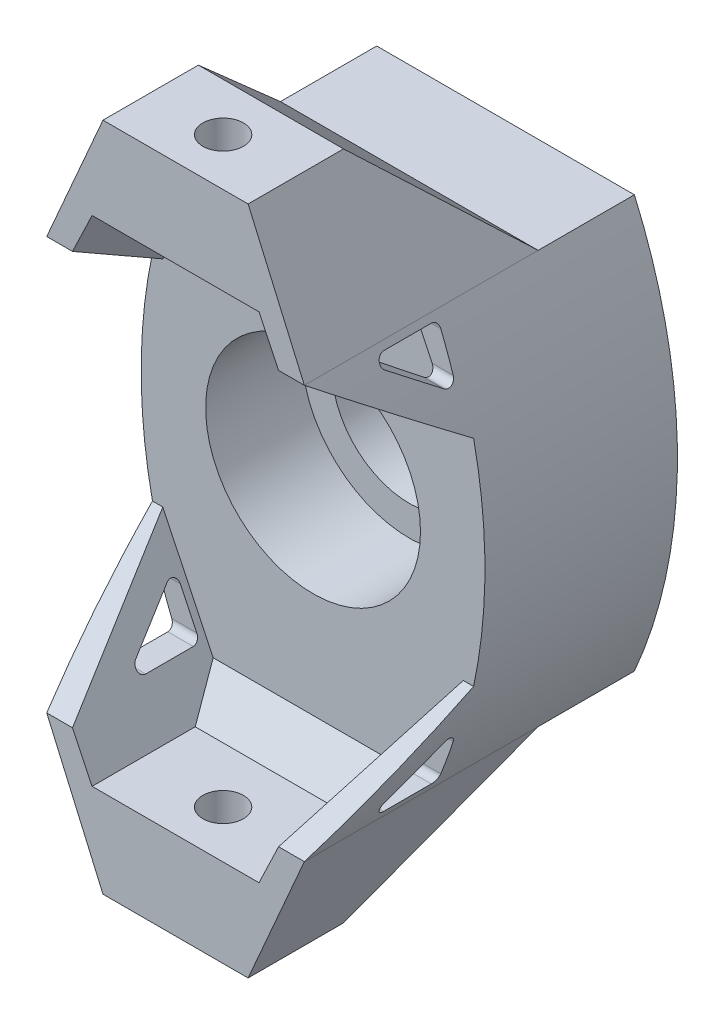
SolidWorks part; units mm, degrees
material "ABS"
ref_plane "Front Plane" through (0, 0, 0) normal (0, 0, 1) x (1, 0, 0)
ref_plane "Top Plane" through (0, 0, 0) normal (0, 1, 0) x (1, 0, 0)
ref_plane "Right Plane" through (0, 0, 0) normal (1, 0, 0) x (0, 0, -1)
sketch "Sketch1" plane through (0, 0, 0) normal (0, 0, 1) x (1, 0, 0)
  line L0 (-9.5192, 15.24) -> (9.5192, 15.24)
  line L1 (-26.1092, 0) -> (27.3943, 0) construction
  line L2 (0, 24.1129) -> (0, -26.203) construction
  line L3 (-9.5192, -15.24) -> (9.5192, -15.24)
  line L4 (-9.5192, 15.24) -> (-5.3622, 24.765)
  line L5 (-5.3622, 24.765) -> (5.3622, 24.765)
  line L6 (5.3622, 24.765) -> (9.5192, 15.24)
  line L7 (5.3622, -24.765) -> (9.5192, -15.24)
  line L8 (-5.3622, -24.765) -> (5.3622, -24.765)
  line L9 (-9.5192, -15.24) -> (-5.3622, -24.765)
  circle A0 centre (0, 0) radius 3.175
  circle A1 centre (0, 0) radius 7.9375
  arc A3 (-9.5192, 15.24) -> (-9.5192, -15.24) centre (25.4, 0) ccw
  arc A4 (9.5192, 15.24) -> (9.5192, -15.24) centre (-25.4, 0) cw
  point P4 (12.7, 0)
  point P14 (-12.7, 0)
  dimension "D1" = 6.35
  dimension "D2" = 15.875
  dimension "D3" = 38.1
  dimension "D5" = 38.1
  dimension "D7" = 12.7
  dimension "D4" = 15.24
  dimension "D6" = 12.7
  dimension "D8" = 9.525
extrude "Boss-Extrude1" add sketch "Sketch1" along normal blind 7.112 contours A4 L0 A3 L3 A1 | L6 L5 L4 L0 | L3 L9 L8 L7
sketch "Sketch2" plane through (0, 0, 0) normal (0, 0, -1) x (-1, 0, 0)
  line L0 (9.5192, -15.24) -> (-9.5192, -15.24) construction
  line L1 (9.5192, 15.24) -> (-9.5192, 15.24) construction
  line L2 (9.5192, -15.24) -> (-9.5192, -15.24)
  line L3 (9.5192, 15.24) -> (-9.5192, 15.24)
  line L6 (-9.5192, -15.24) -> (-5.3622, -24.765)
  line L7 (-5.3622, -24.765) -> (5.3622, -24.765)
  line L8 (5.3622, -24.765) -> (9.5192, -15.24)
  line L9 (9.5192, 15.24) -> (5.3622, 24.765)
  line L10 (5.3622, 24.765) -> (-5.3622, 24.765)
  line L11 (-5.3622, 24.765) -> (-9.5192, 15.24)
  line L12 (-9.5192, -15.24) -> (-5.3622, -24.765)
  line L13 (-5.3622, -24.765) -> (5.3622, -24.765)
  line L14 (5.3622, -24.765) -> (9.5192, -15.24)
  line L15 (9.5192, 15.24) -> (5.3622, 24.765)
  line L16 (5.3622, 24.765) -> (-5.3622, 24.765)
  line L17 (-5.3622, 24.765) -> (-9.5192, 15.24)
  arc A2 (-9.5192, 15.24) -> (-9.5192, -15.24) centre (25.4, 0) ccw
  arc A3 (9.5192, -15.24) -> (9.5192, 15.24) centre (-25.4, 0) ccw
  arc A4 (-9.5192, 15.24) -> (-9.5192, -15.24) centre (25.4, 0) ccw
  arc A5 (9.5192, -15.24) -> (9.5192, 15.24) centre (-25.4, 0) ccw
  circle A6 centre (0, 0) radius 5.715
  circle A8 centre (0, 0) radius 3.175 construction
  circle A9 centre (0, 0) radius 3.175
  dimension "D2" = 2.54
  dimension "D1" = 0
extrude "Boss-Extrude2" add sketch "Sketch2" along normal blind 7.112
sketch "Sketch3" plane through (0, 0, 7.112) normal (0, 0, 1) x (1, 0, 0)
  line L0 (5.3622, 24.765) -> (9.5192, 15.24) construction
  line L1 (-5.3622, 24.765) -> (5.3622, 24.765) construction
  line L2 (0, 24.1129) -> (0, -26.203) construction
  line L3 (-9.5192, 15.24) -> (9.5192, 15.24) construction
  line L4 (-9.5192, 15.24) -> (-5.3622, 24.765) construction
  line L5 (5.3622, 24.765) -> (9.5192, 15.24)
  line L6 (-5.3622, 24.765) -> (5.3622, 24.765)
  line L7 (0, 24.1129) -> (0, -26.203)
  line L8 (-9.5192, 15.24) -> (9.5192, 15.24)
  line L9 (-9.5192, 15.24) -> (-5.3622, 24.765)
  line L10 (5.3622, -24.765) -> (9.5192, -15.24) construction
  line L11 (-5.3622, -24.765) -> (5.3622, -24.765) construction
  line L12 (-9.5192, -15.24) -> (-5.3622, -24.765) construction
  line L13 (-9.5192, -15.24) -> (9.5192, -15.24) construction
  line L14 (5.3622, -24.765) -> (9.5192, -15.24)
  line L15 (-5.3622, -24.765) -> (5.3622, -24.765)
  line L16 (-9.5192, -15.24) -> (-5.3622, -24.765)
  line L17 (-9.5192, -15.24) -> (9.5192, -15.24)
extrude "Boss-Extrude3" add sketch "Sketch3" along normal blind 10.16
sketch "Sketch4" plane through (0, 24.765, 0) normal (0, 1, 0) x (1, 0, 0)
  line L0 (0, 0) -> (0, -17.272) construction
  line L1 (5.3622, -17.272) -> (-5.3622, -17.272) construction
  line L2 (-5.3622, -13.7567) -> (5.3622, -13.7567) construction
  line L3 (-5.3622, -17.272) -> (-5.3622, 0) construction
  line L4 (5.3622, -17.272) -> (5.3622, 0) construction
  circle A0 centre (0, -13.7567) radius 1.5
  dimension "D2" = 3
  dimension "D1" = 3.5153
extrude "Cut-Extrude1" cut sketch "Sketch4" against normal through all
sketch3d "3DSketch1"
  line L1 (-9.5192, 15.24, 17.272) -> (-9.5192, 15.24, 7.112) construction
sketch "Sketch5" plane through (-9.5192, 0, 0) normal (-1, 0, 0) x (0, 0, 1)
  line L0 (17.272, 24.765) -> (17.272, 15.24) construction
  line L1 (7.112, 15.24) -> (0, 15.24) construction
  line L2 (17.272, 15.24) -> (7.112, 15.24) construction
  line L3 (17.272, 24.765) -> (0, 24.765) construction
  line L4 (0, 24.765) -> (0, 15.24) construction
  line L5 (17.272, 24.765) -> (17.272, 15.24)
  line L6 (7.112, 15.24) -> (0, 15.24)
  line L7 (17.272, 15.24) -> (7.112, 15.24)
  line L8 (17.272, 24.765) -> (0, 24.765)
  line L9 (0, 24.765) -> (0, 15.24)
  line L10 (15.2567, 24.765) -> (12.2567, 24.765) construction
  line L11 (15.2567, 24.765) -> (12.2567, 24.765)
  line L12 (12.2567, 24.765) -> (10.2247, 24.765)
  line L13 (17.272, 18.2651) -> (9.652, 18.2651)
  line L14 (7.112, 15.7251) -> (7.112, 15.24)
  line L15 (7.112, 15.7251) -> (9.652, 18.2651)
  line L16 (0, 15.24) -> (10.2247, 24.765)
  dimension "D5" = 45
  dimension "D1" = 2.0153
  dimension "D2" = 2.032
  dimension "D4" = 6.4999
  dimension "D6" = 2.54
extrude "Cut-Extrude2" cut sketch "Sketch5" against normal through all contours L9 L16 L8 | L15 L14 L7 L5 L13
sketch "Sketch6" plane through (0, 0, 7.112) normal (0, 0, 1) x (1, 0, 0)
  line L0 (-9.5192, 15.24) -> (9.5192, 15.24) construction
  line L1 (-9.5192, 15.24) -> (9.5192, 15.24)
  line L2 (-11.864, 7.9375) -> (11.864, 7.9375)
  line L3 (-6.1669, 18.2651) -> (-6.1669, 7.9375)
  line L4 (6.1669, 18.2651) -> (6.1669, 7.9375)
  line L5 (8.1989, 18.2651) -> (-8.1989, 18.2651) construction
  line L6 (8.1989, 18.2651) -> (-8.1989, 18.2651)
  line L7 (-9.3075, 15.7251) -> (-8.1989, 18.2651) construction
  line L8 (-9.3075, 15.7251) -> (-9.5192, 15.24) construction
  line L9 (-9.3075, 15.7251) -> (-8.1989, 18.2651)
  line L10 (-9.3075, 15.7251) -> (-9.5192, 15.24)
  line L11 (8.1989, 18.2651) -> (9.3075, 15.7251) construction
  line L12 (9.5192, 15.24) -> (9.3075, 15.7251) construction
  line L13 (8.1989, 18.2651) -> (9.3075, 15.7251)
  line L14 (9.5192, 15.24) -> (9.3075, 15.7251)
  line L15 (-11.102, 7.9375) -> (-6.1669, 18.2651)
  line L16 (6.1669, 18.2651) -> (11.102, 7.9375)
  arc A0 (9.5192, -15.24) -> (9.5192, 15.24) centre (-25.4, 0) ccw construction
  arc A1 (-9.5192, 15.24) -> (-9.5192, -15.24) centre (25.4, 0) ccw construction
  arc A2 (9.5192, -15.24) -> (9.5192, 15.24) centre (-25.4, 0) ccw
  arc A3 (-9.5192, 15.24) -> (-9.5192, -15.24) centre (25.4, 0) ccw
  circle A4 centre (0, 0) radius 7.9375 construction
  circle A5 centre (0, 0) radius 7.9375
  arc M3 (9.5192, -15.24) -> (9.5192, 15.24) centre (-25.4, 0) ccw
  line M4 (9.5192, 15.24) -> (9.3075, 15.7251)
  line M5 (9.3075, 15.7251) -> (-9.3075, 15.7251)
  line M6 (-9.3075, 15.7251) -> (-9.5192, 15.24)
  arc M7 (-9.5192, 15.24) -> (-9.5192, -15.24) centre (25.4, 0) ccw
  dimension "D1" = 2.032
  dimension "D2" = 2.032
  dimension "D3" = 0.762
  dimension "D4" = 0.762
extrude "Boss-Extrude5" add sketch "Sketch6" along normal up to surface (10.16 mm away) contours L2 L15 L1 M7 | L1 L15 M5 M6 | L15 L6 L9 M5 | L6 L16 L13 M5 | L16 L1 M5 M4 | L1 L16 L2 M3 up to face at (0, 21.5151, 17.272)
sketch "Sketch7" plane through (-9.5192, 0, 0) normal (-1, 0, 0) x (0, 0, 1)
  line L0 (7.112, 7.9375) -> (7.112, 15.24)
  line L1 (17.272, 15.24) -> (0, 15.24) construction
  line L2 (7.112, 9.7631) -> (14.732, 15.24)
  line L4 (7.112, 7.9375) -> (17.272, 15.24)
  line L11 (17.272, 15.24) -> (17.272, 7.9375)
  line L12 (17.272, 7.9375) -> (7.112, 7.9375) construction
  line L13 (17.272, 7.9375) -> (7.112, 7.9375)
  line L23 (8.4038, 11.3074) -> (11.9191, 13.834)
  line L24 (7.612, 7.9375) -> (7.612, 15.24) construction
  line L25 (7.612, 11.7134) -> (7.612, 14.24)
  line L26 (11.6273, 14.74) -> (8.112, 14.74)
  arc A0 (11.6273, 14.74) -> (11.9191, 13.834) centre (11.6273, 14.24) cw
  arc A1 (7.612, 11.7134) -> (8.4038, 11.3074) centre (8.112, 11.7134) ccw
  arc A2 (7.612, 14.24) -> (8.112, 14.74) centre (8.112, 14.24) cw
  point P2 (6.8202, 10.1691)
  point P7 (14.4402, 15.646)
  dimension "D5" = 0.5
  dimension "D1" = 2.54
  dimension "D2" = 0.5
  dimension "D3" = 0.5
  dimension "D4" = 0.5
extrude "Cut-Extrude3" cut sketch "Sketch7" against normal through all and the other way through all contours L13 L11 L4
sketch "Sketch8" plane through (0, 0, 17.272) normal (0, 0, 1) x (1, 0, 0)
  line L0 (-6.1669, 18.2651) -> (-6.1669, 7.9375) construction
  line L1 (-11.102, 7.9375) -> (-6.1669, 18.2651) construction
  line L2 (-11.864, 7.9375) -> (11.864, 7.9375) construction
  line L3 (-9.5192, 15.24) -> (9.5192, 15.24) construction
  line L4 (-9.3075, 15.7251) -> (-9.5192, 15.24) construction
  line L5 (-9.3075, 15.7251) -> (-8.1989, 18.2651) construction
  line L6 (8.1989, 18.2651) -> (-8.1989, 18.2651) construction
  line L7 (8.1989, 18.2651) -> (9.3075, 15.7251) construction
  line L8 (9.5192, 15.24) -> (9.3075, 15.7251) construction
  line L9 (6.1669, 18.2651) -> (6.1669, 7.9375) construction
  line L10 (6.1669, 18.2651) -> (11.102, 7.9375) construction
  line L11 (-6.1669, 18.2651) -> (-6.1669, 7.9375)
  line L12 (-11.102, 7.9375) -> (-6.1669, 18.2651)
  line L13 (-11.864, 7.9375) -> (11.864, 7.9375)
  line L14 (-9.5192, 15.24) -> (9.5192, 15.24)
  line L15 (-9.3075, 15.7251) -> (-9.5192, 15.24)
  line L16 (-9.3075, 15.7251) -> (-8.1989, 18.2651)
  line L17 (8.1989, 18.2651) -> (-8.1989, 18.2651)
  line L18 (8.1989, 18.2651) -> (9.3075, 15.7251)
  line L19 (9.5192, 15.24) -> (9.3075, 15.7251)
  line L20 (6.1669, 18.2651) -> (6.1669, 7.9375)
  line L21 (6.1669, 18.2651) -> (11.102, 7.9375)
  line L22 (-26.1092, 0) -> (27.3943, 0) construction
  line L23 (-26.1092, 0) -> (27.3943, 0)
  line L24 (6.1669, -18.2651) -> (11.102, -7.9375)
  line L25 (-11.864, -7.9375) -> (11.864, -7.9375)
  line L26 (8.1989, -18.2651) -> (-8.1989, -18.2651)
  line L27 (-9.3075, -15.7251) -> (-8.1989, -18.2651)
  line L28 (-9.3075, -15.7251) -> (-9.5192, -15.24)
  line L29 (-9.5192, -15.24) -> (9.5192, -15.24)
  line L30 (-11.102, -7.9375) -> (-6.1669, -18.2651)
  arc A0 (-9.5192, 15.24) -> (-9.5192, -15.24) centre (25.4, 0) ccw construction
  circle A1 centre (0, 0) radius 7.9375
  circle A2 centre (0, 0) radius 7.9375
  arc A3 (9.5192, -15.24) -> (9.5192, 15.24) centre (-25.4, 0) ccw construction
  arc A4 (-9.5192, 15.24) -> (-9.5192, -15.24) centre (25.4, 0) ccw
  arc A5 (9.5192, -15.24) -> (9.5192, 15.24) centre (-25.4, 0) ccw
  line M12 (9.5192, -15.24) -> (-9.5192, -15.24)
  dimension "D1" = 0
sketch "Sketch9" plane through (-9.5192, 0, 0) normal (-1, 0, 0) x (0, 0, 1)
  line L0 (-10.969, 0) -> (23.2559, 0) construction
  line L1 (7.112, 15.7251) -> (7.112, 15.24) construction
  line L2 (0, 15.24) -> (10.2247, 24.765) construction
  line L3 (7.112, 15.24) -> (0, 15.24) construction
  line L4 (17.272, 15.24) -> (7.112, 15.24) construction
  line L5 (7.112, 15.7251) -> (9.652, 18.2651) construction
  line L6 (17.272, 18.2651) -> (9.652, 18.2651) construction
  line L7 (17.272, 24.765) -> (17.272, 15.24) construction
  line L8 (17.272, 24.765) -> (0, 24.765) construction
  line L9 (0, 24.765) -> (0, 15.24) construction
  line L10 (7.112, 15.7251) -> (7.112, 15.24)
  line L11 (0, 15.24) -> (10.2247, 24.765)
  line L12 (7.112, 15.24) -> (0, 15.24)
  line L13 (17.272, 15.24) -> (7.112, 15.24)
  line L14 (7.112, 15.7251) -> (9.652, 18.2651)
  line L15 (17.272, 18.2651) -> (9.652, 18.2651)
  line L16 (17.272, 24.765) -> (17.272, 15.24)
  line L17 (17.272, 24.765) -> (0, 24.765)
  line L18 (0, 24.765) -> (0, 15.24)
  line L19 (17.272, -24.765) -> (0, -24.765)
  line L20 (17.272, -24.765) -> (17.272, -15.24)
  line L21 (17.272, -18.2651) -> (9.652, -18.2651)
  line L22 (0, -15.24) -> (10.2247, -24.765)
  line L23 (0, -24.765) -> (0, -15.24)
  line L24 (7.112, -15.24) -> (0, -15.24)
  line L25 (7.112, -15.7251) -> (9.652, -18.2651)
  line L26 (7.112, -15.7251) -> (7.112, -15.24)
  point P3 (7.112, 15.24)
  point P4 (7.112, 15.7251)
extrude "Cut-Extrude5" cut sketch "Sketch9" against normal through all contours L23 L19 L22
extrude "Cut-Extrude6" cut sketch "Sketch8" against normal up to surface (10.16 mm away) contours L30 L26 L24 M12 up to face at (7.9375, 0, 7.112)
sketch "Sketch10" plane through (0, 0, 7.112) normal (0, 0, 1) x (1, 0, 0)
  line L0 (5.3622, -24.765) -> (9.5192, -15.24) construction
  line L1 (6.1669, -18.2651) -> (11.102, -7.9375) construction
  line L2 (8.1989, -18.2651) -> (-8.1989, -18.2651) construction
  line L3 (-9.3075, -15.7251) -> (-9.5192, -15.24) construction
  line L4 (-9.3075, -15.7251) -> (-8.1989, -18.2651) construction
  line L5 (-11.864, -7.9375) -> (11.864, -7.9375) construction
  line L6 (-11.102, -7.9375) -> (-6.1669, -18.2651) construction
  line L7 (8.1989, -18.2651) -> (9.5192, -15.24)
  line L8 (6.1669, -18.2651) -> (11.102, -7.9375)
  line L9 (8.1989, -18.2651) -> (-8.1989, -18.2651)
  line L10 (-9.3075, -15.7251) -> (-9.5192, -15.24)
  line L11 (-9.3075, -15.7251) -> (-8.1989, -18.2651)
  line L12 (-11.864, -7.9375) -> (11.864, -7.9375)
  line L13 (-11.102, -7.9375) -> (-6.1669, -18.2651)
  arc A0 (9.5192, -15.24) -> (9.5192, 15.24) centre (-25.4, 0) ccw construction
  arc A1 (-9.5192, 15.24) -> (-9.5192, -15.24) centre (25.4, 0) ccw construction
  arc A2 (9.5192, -15.24) -> (9.5192, 15.24) centre (-25.4, 0) ccw
  arc A3 (-9.5192, 15.24) -> (-9.5192, -15.24) centre (25.4, 0) ccw
  arc M4 (-11.864, 7.9375) -> (-9.5192, -15.24) centre (25.4, 0) ccw
  line M5 (-9.5192, -15.24) -> (-7.6125, -15.24)
  line M9 (7.6125, -15.24) -> (9.5192, -15.24)
  arc M10 (9.5192, -15.24) -> (11.864, 7.9375) centre (-25.4, 0) ccw
extrude "Boss-Extrude6" add sketch "Sketch10" along normal up to surface (10.16 mm away) contours L13 L12 M4 M5 | L12 L8 M9 M10 up to face at (0, -18.3775, 17.272)
sketch "Sketch11" plane through (-9.5192, 0, 0) normal (-1, 0, 0) x (0, 0, 1)
  line L0 (17.272, 15.24) -> (0, 15.24) construction
  line L1 (7.112, 7.9375) -> (17.272, 15.24) construction
  line L2 (7.112, 9.7631) -> (14.732, 15.24) construction
  line L3 (11.6273, 14.74) -> (8.112, 14.74) construction
  line L4 (8.4038, 11.3074) -> (11.9191, 13.834) construction
  line L5 (7.612, 11.7134) -> (7.612, 14.24) construction
  line L6 (7.112, 7.9375) -> (7.112, 15.24) construction
  line L7 (17.272, 15.24) -> (0, 15.24)
  line L8 (7.112, 7.9375) -> (17.272, 15.24)
  line L9 (7.112, 9.7631) -> (14.732, 15.24)
  line L10 (11.6273, 14.74) -> (8.112, 14.74)
  line L11 (8.4038, 11.3074) -> (11.9191, 13.834)
  line L12 (7.612, 11.7134) -> (7.612, 14.24)
  line L13 (7.112, 7.9375) -> (7.112, 15.24)
  line L14 (-9.8856, 0) -> (19.3869, 0) construction
  line L15 (7.112, -7.9375) -> (17.272, -15.24)
  line L16 (7.112, -7.9375) -> (7.112, -15.24)
  line L17 (17.272, -15.24) -> (0, -15.24)
  line L18 (7.112, -9.7631) -> (14.732, -15.24)
  line L19 (8.4038, -11.3074) -> (11.9191, -13.834)
  line L20 (7.612, -11.7134) -> (7.612, -14.24)
  line L21 (11.6273, -14.74) -> (8.112, -14.74)
  line L22 (17.272, -15.24) -> (17.272, -7.9375) construction
  line L23 (17.272, -7.9375) -> (7.112, -7.9375) construction
  line L24 (17.272, -15.24) -> (17.272, -7.9375)
  line L25 (17.272, -7.9375) -> (7.112, -7.9375)
  arc A0 (11.9191, 13.834) -> (11.6273, 14.74) centre (11.6273, 14.24) ccw construction
  arc A1 (7.612, 11.7134) -> (8.4038, 11.3074) centre (8.112, 11.7134) ccw construction
  arc A2 (8.112, 14.74) -> (7.612, 14.24) centre (8.112, 14.24) ccw construction
  arc A3 (11.9191, 13.834) -> (11.6273, 14.74) centre (11.6273, 14.24) ccw
  arc A4 (7.612, 11.7134) -> (8.4038, 11.3074) centre (8.112, 11.7134) ccw
  arc A5 (8.112, 14.74) -> (7.612, 14.24) centre (8.112, 14.24) ccw
  arc A6 (11.9191, -13.834) -> (11.6273, -14.74) centre (11.6273, -14.24) cw
  arc A7 (7.612, -11.7134) -> (8.4038, -11.3074) centre (8.112, -11.7134) cw
  arc A8 (8.112, -14.74) -> (7.612, -14.24) centre (8.112, -14.24) cw
extrude "Cut-Extrude7" cut sketch "Sketch11" against normal through all and the other way through all contours L24 L25 L15 | A8 L21 A6 L19 A7 L20
sketch "Sketch12" plane through (-9.5192, 0, 0) normal (-1, 0, 0) x (0, 0, 1)
  line L0 (7.112, 15.7251) -> (7.112, 15.24) construction
  line L1 (7.112, 15.7251) -> (9.652, 18.2651) construction
  line L2 (7.112, 15.7251) -> (7.112, 15.24)
  line L3 (7.112, 15.7251) -> (9.652, 18.2651)
  line L4 (7.112, 15.24) -> (0, 15.24) construction
  line L5 (7.112, 15.24) -> (0, 15.24)
  line L6 (-10.8614, 0) -> (18.6108, 0) construction
  line L7 (7.112, -15.7251) -> (9.652, -18.2651)
  line L8 (7.112, -15.7251) -> (7.112, -15.24)
  line L9 (7.112, -15.24) -> (0, -15.24)
  line L10 (9.652, -18.2651) -> (7.112, -18.2651)
  line L11 (7.112, -18.2651) -> (7.112, -15.7251)
extrude "Boss-Extrude7" add sketch "Sketch12" along normal up to surface (14.3659 mm away) from surface contours L11 L10 L7
